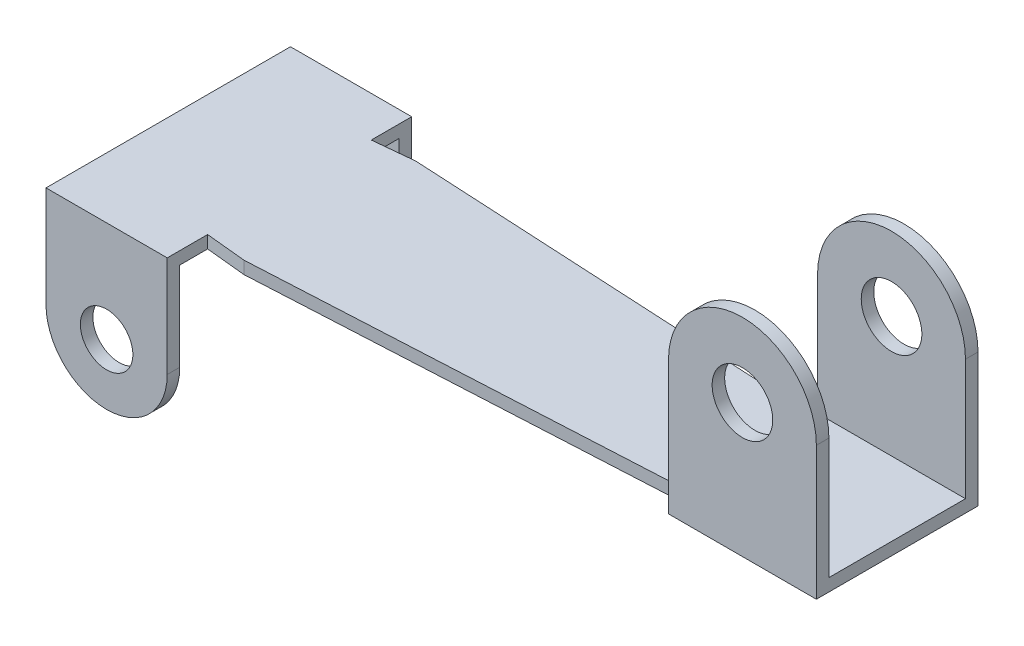
SolidWorks part; units mm, degrees
ref_plane "Front Plane" through (0, 0, 0) normal (0, 0, 1) x (1, 0, 0)
ref_plane "Top Plane" through (0, 0, 0) normal (0, 1, 0) x (1, 0, 0)
ref_plane "Right Plane" through (0, 0, 0) normal (1, 0, 0) x (0, 0, -1)
sketch "Sketch1" plane through (0, 0, 0) normal (0, 1, 0) x (1, 0, 0)
  line L0 (0, 3.025) -> (0, -3.025)
  line L1 (0, 3.025) -> (3, 3.025)
  line L2 (3, 3.025) -> (3, 2.025)
  line L3 (3, 2.025) -> (4, 2.125)
  line L4 (4, 2.125) -> (14.38, 1.575)
  line L5 (14.38, 1.575) -> (14.38, 2)
  line L6 (14.38, 2) -> (18.04, 2)
  line L7 (18.04, 2) -> (18.04, -2)
  line L8 (14.38, -1.575) -> (4, -2.125)
  line L9 (4, -2.125) -> (3, -2.025)
  line L10 (3, -2.025) -> (3, -3.025)
  line L11 (3, -3.025) -> (0, -3.025)
  line L12 (18.04, -2) -> (14.38, -2)
  line L13 (14.38, -2) -> (14.38, -1.575)
  point P14 (18.04, 0)
  dimension "D1" = 6.05
  dimension "D2" = 3
  dimension "D3" = 1
  dimension "D4" = 4.25
  dimension "D5" = 3.15
  dimension "D6" = 4
  dimension "D7" = 3.66
  dimension "D8" = 18.04
  dimension "D9" = 1
extrude "Boss-Extrude1" add sketch "Sketch1" along normal blind 0.31
sketch "Sketch2" plane through (0, 0.31, 0) normal (0, 1, 0) x (1, 0, 0)
  line L0 (3, 2.025) -> (3, 3.025) construction
  line L1 (0, 3.025) -> (3, 3.025)
  line L2 (0, 3.025) -> (0, 2.715)
  line L3 (0, 2.715) -> (3, 2.715)
  line L4 (3, 3.025) -> (3, 2.715)
  line L5 (0, 3.025) -> (0, -3.025) construction
  line L6 (3, -3.025) -> (0, -3.025)
  line L7 (3, -3.025) -> (3, -2.715)
  line L8 (3, -2.715) -> (0, -2.715)
  line L9 (0, -3.025) -> (0, -2.715)
  dimension "D1" = 0.31
extrude "Boss-Extrude2" add sketch "Sketch2" against normal blind 4
sketch "Sketch3" plane through (0, 0, 3.025) normal (0, 0, 1) x (1, 0, 0)
  line L0 (0, 0.31) -> (0, -3.69) construction
  line L1 (3, 0.31) -> (3, -3.69) construction
  line L2 (0, -3.69) -> (3, -3.69) construction
  line L3 (0, -2.19) -> (0, -3.69)
  line L4 (0, -3.69) -> (3, -3.69)
  line L5 (3, -3.69) -> (3, -2.19)
  arc A0 (0, -2.19) -> (3, -2.19) centre (1.5, -2.19) ccw
  circle A1 centre (1.5, -2.19) radius 0.65
  line M1 (0, 0.31) -> (0, -3.69)
  line M2 (0, -3.69) -> (3, -3.69)
  line M3 (3, -3.69) -> (3, 0.31)
  dimension "D1" = 1.3
extrude "Cut-Extrude1" cut sketch "Sketch3" against normal blind 11 contours A1 | A0 L4 M3 | A0 M1 M2
sketch "Sketch4" plane through (0, 0.31, 0) normal (0, 1, 0) x (1, 0, 0)
  line L0 (18.04, -2) -> (18.04, 2) construction
  line L1 (14.38, 2) -> (18.04, 2)
  line L2 (14.38, 2) -> (14.38, 1.69)
  line L3 (14.38, 1.69) -> (18.04, 1.69)
  line L4 (18.04, 2) -> (18.04, 1.69)
  line L6 (14.38, -2) -> (18.04, -2)
  line L7 (14.38, -2) -> (14.38, -1.69)
  line L8 (14.38, -1.69) -> (18.04, -1.69)
  line L9 (18.04, -2) -> (18.04, -1.69)
  dimension "D1" = 0.31
extrude "Boss-Extrude3" add sketch "Sketch4" along normal blind 4.82
sketch "Sketch5" plane through (0, 0, -2) normal (0, 0, -1) x (-1, 0, 0)
  line L0 (-18.04, 5.13) -> (-18.04, 0) construction
  line L1 (-14.38, 5.13) -> (-14.38, 0) construction
  line L2 (-18.04, 5.13) -> (-14.38, 5.13) construction
  line L3 (-18.04, 3.3) -> (-18.04, 5.13)
  line L4 (-18.04, 5.13) -> (-14.38, 5.13)
  line L5 (-14.38, 5.13) -> (-14.38, 3.3)
  circle A0 centre (-16.21, 3.3) radius 0.75
  arc A1 (-18.04, 3.3) -> (-14.38, 3.3) centre (-16.21, 3.3) cw
  line M2 (-14.38, 0) -> (-14.38, 5.13)
  line M3 (-14.38, 5.13) -> (-18.04, 5.13)
  line M4 (-18.04, 5.13) -> (-18.04, 0)
  dimension "D1" = 1.5
extrude "Cut-Extrude2" cut sketch "Sketch5" against normal blind 4.82 contours A1 L4 M4 | A1 M3 M2 | A0
